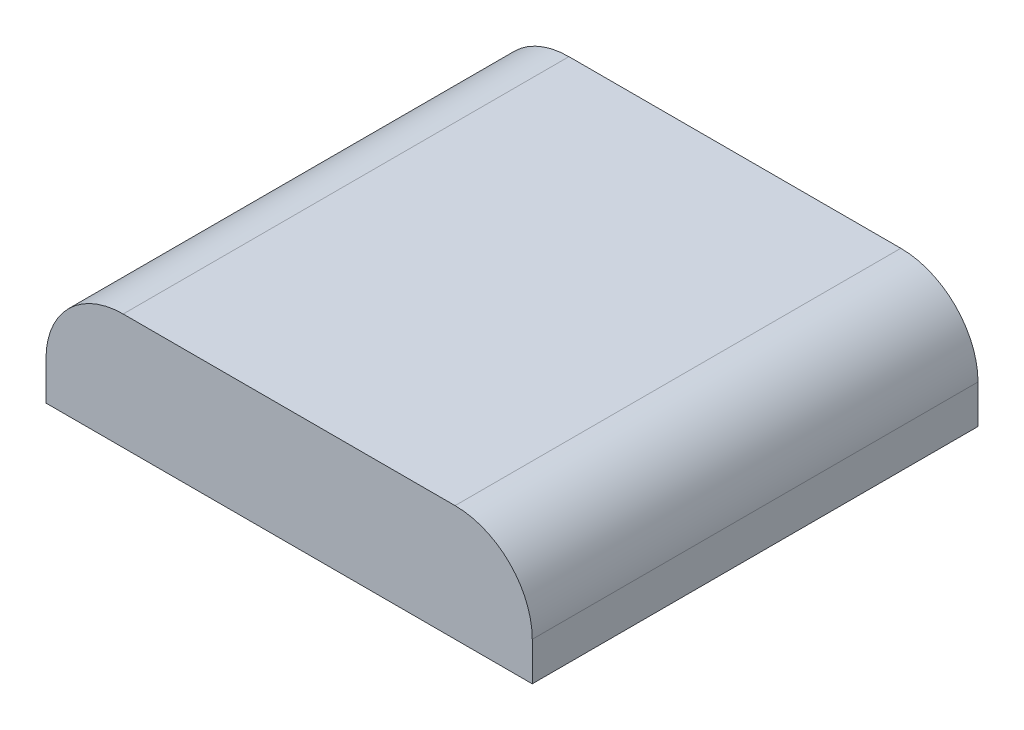
SolidWorks part; units mm, degrees
material "ABS"
ref_plane "Front Plane" through (0, 0, 0) normal (0, 0, 1) x (1, 0, 0)
ref_plane "Top Plane" through (0, 0, 0) normal (0, 1, 0) x (1, 0, 0)
ref_plane "Right Plane" through (0, 0, 0) normal (1, 0, 0) x (0, 0, -1)
sketch "Sketch1" plane through (0, 0, 0) normal (0, 1, 0) x (1, 0, 0)
  line L1 (-31.5, 28.875) -> (31.5, 28.875)
  line L2 (-31.5, 28.875) -> (-31.5, -28.875)
  line L3 (-31.5, -28.875) -> (31.5, -28.875)
  line L4 (31.5, 28.875) -> (31.5, -28.875)
  line L5 (-31.5, 28.875) -> (31.5, -28.875) construction
  line L6 (-31.5, -28.875) -> (31.5, 28.875) construction
  point P0 (0, 0)
  dimension "D1" = 63
  dimension "D2" = 57.75
extrude "Boss-Extrude1" add sketch "Sketch1" along normal blind 15
fillet "Fillet1" radius 10 2 edges at (31.5, 15, 0) (-31.5, 15, 0)
